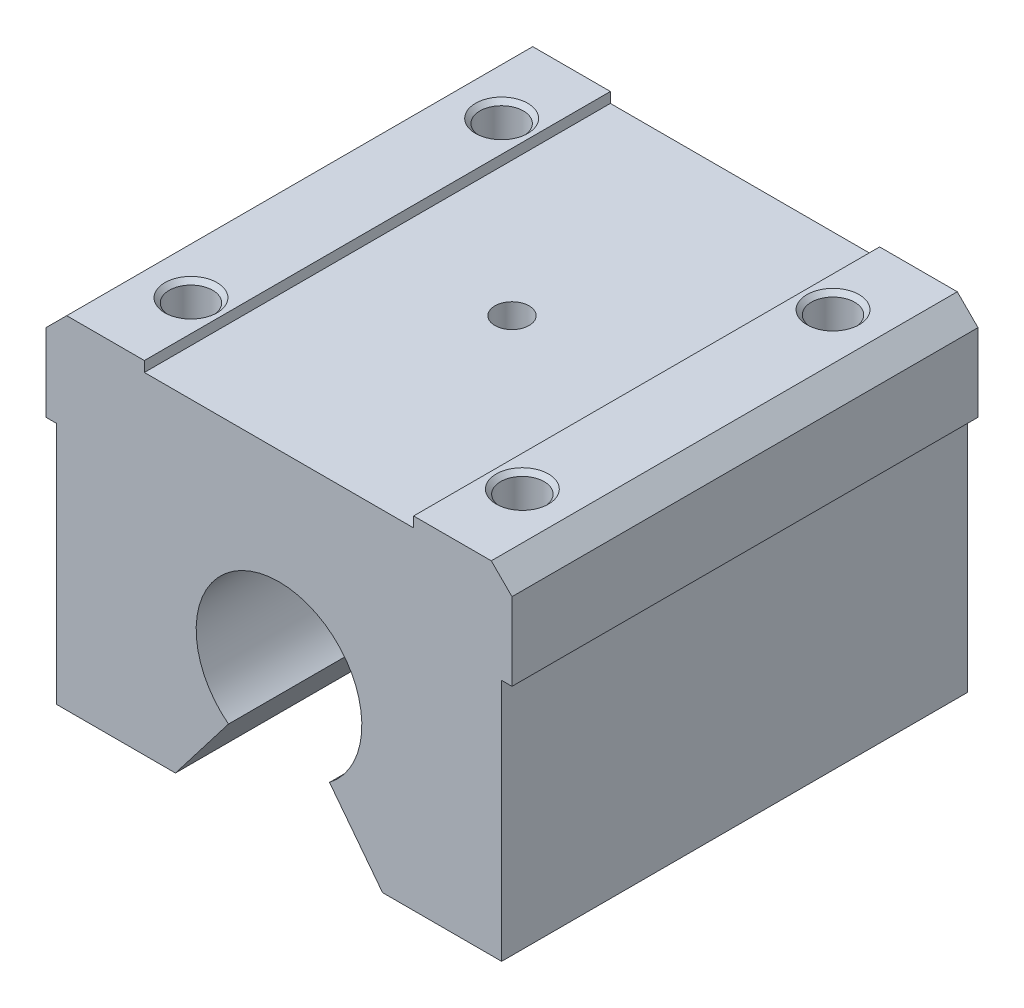
SolidWorks part; units mm, degrees
ref_plane "Front Plane" through (0, 0, 0) normal (0, 0, 1) x (1, 0, 0)
ref_plane "Top Plane" through (0, 0, 0) normal (0, 1, 0) x (1, 0, 0)
ref_plane "Right Plane" through (0, 0, 0) normal (1, 0, 0) x (0, 0, -1)
sketch "Sketch1" plane through (0, 0, 0) normal (0, 0, 1) x (1, 0, 0)
  line L0 (0, 0) -> (0, 37.2391) construction
  line L1 (0, 0) -> (27.9005, 0) construction
  line L2 (10, -13) -> (21.5, -13)
  line L3 (21.5, -13) -> (21.5, 10.5)
  line L4 (21.5, 10.5) -> (22.5, 10.5)
  line L5 (22.5, 10.5) -> (22.5, 18)
  line L6 (22.5, 18) -> (20.5, 20)
  line L7 (20.5, 20) -> (13, 20)
  line L8 (13, 20) -> (13, 19)
  line L9 (13, 19) -> (0, 19)
  line L10 (21.5, 10.5) -> (21.5, 19) construction
  line L11 (0, 8) -> (0, 19)
  line L12 (4.8777, -6.341) -> (10, -13)
  line L13 (16, 26.894) -> (16, 15.2711) construction
  circle A0 centre (0, 0) radius 8
  dimension "D1" = 16
  dimension "D2" = 45
  dimension "D3" = 33
  dimension "D4" = 20
  dimension "D5" = 45
  dimension "D6" = 1
  dimension "D7" = 1
  dimension "D8" = 20
  dimension "D9" = 32
  dimension "D10" = 6
sketch "Sketch2" plane through (0, 0, 0) normal (0, 0, 1) x (1, 0, 0)
  line L0 (0, 8) -> (0, 19) construction
  line L1 (13, 19) -> (0, 19) construction
  line L2 (13, 20) -> (13, 19) construction
  line L3 (20.5, 20) -> (13, 20) construction
  line L4 (22.5, 18) -> (20.5, 20) construction
  line L5 (22.5, 10.5) -> (22.5, 18) construction
  line L6 (21.5, 10.5) -> (22.5, 10.5) construction
  line L7 (21.5, -13) -> (21.5, 10.5) construction
  line L8 (10, -13) -> (21.5, -13) construction
  line L9 (4.8777, -6.341) -> (10, -13) construction
  line L10 (0, 8) -> (0, 19) construction
  line L11 (13, 19) -> (-13, 19)
  line L12 (13, 20) -> (13, 19)
  line L13 (20.5, 20) -> (13, 20)
  line L14 (22.5, 18) -> (20.5, 20)
  line L15 (22.5, 10.5) -> (22.5, 18)
  line L16 (21.5, 10.5) -> (22.5, 10.5)
  line L17 (21.5, -13) -> (21.5, 10.5)
  line L18 (10, -13) -> (21.5, -13)
  line L19 (4.8777, -6.341) -> (10, -13)
  line L20 (-4.8777, -6.341) -> (-10, -13)
  line L21 (-10, -13) -> (-21.5, -13)
  line L22 (-21.5, -13) -> (-21.5, 10.5)
  line L23 (-21.5, 10.5) -> (-22.5, 10.5)
  line L24 (-22.5, 10.5) -> (-22.5, 18)
  line L25 (-22.5, 18) -> (-20.5, 20)
  line L26 (-20.5, 20) -> (-13, 20)
  line L27 (-13, 20) -> (-13, 19)
  circle A1 centre (0, 0) radius 8
  arc A2 (4.8777, -6.341) -> (-4.8777, -6.341) centre (0, 0) ccw
  dimension "D1" = 0
extrude "Boss-Extrude1" add sketch "Sketch2" along normal mid plane 45
hole_wizard "M5 Tapped Hole1" positions "Sketch3" profile "Sketch4" tap size "M5" standard "ISO"
sketch "Sketch3" plane through (0, 20, 0) normal (0, 1, 0) x (1, 0, 0)
  line L0 (0, 0) -> (0, 23.9789) construction
  line L1 (-8, 0) -> (8, 0) construction
  line L4 (0, 0) -> (-26.7272, 0) construction
  point P0 (-16, 15)
  point P14 (16, 15)
  point P16 (-16, -15)
  point P17 (16, -15)
  dimension "D1" = 32
  dimension "D2" = 30
sketch "Sketch4" plane through (-16, 20, -15) normal (1, 0, 0) x (0, 0, 1)
  line L0 (0, 0) -> (0, 13.6618)
  line L1 (0, 13.6618) -> (2.1, 12.4)
  line L2 (2.1, 12.4) -> (2.1, 0.425)
  line L3 (2.1, 0.425) -> (2.525, 0)
  line L5 (2.525, 0) -> (0, 0)
  line L6 (-2.1, 0.425) -> (-2.525, 0) construction
  line L10 (0, 13.6618) -> (-2.1, 12.4) construction
  line L11 (0, -6.35) -> (0, 107.95) construction
  dimension "Tap Drill Dia." = 4.2
  dimension "Tap Drill Depth" = 12.4
  dimension "Near C'Sink Dia." = 5.05
  dimension "Near C'Sink Angle" = 90
  dimension "Drill Angle" = 118
cosmetic thread "Hole Thread1" parameters "D1"=10, "D2"=5
cosmetic thread "Hole Thread2" parameters "D1"=10, "D2"=5
cosmetic thread "Hole Thread3" parameters "D1"=10, "D2"=5
cosmetic thread "Hole Thread4" parameters "D1"=10, "D2"=5
sketch "Sketch5" [suppressed] plane through (0, 0, 0) normal (0, 0, 1) x (1, 0, 0)
  circle A0 centre (0, 0) radius 8 construction
  circle A1 centre (0, 0) radius 8
extrude "Boss-Extrude2" [suppressed] add sketch "Sketch5" along normal mid plane 600
ref_plane "Plane1" [suppressed] through (0, -8, 0) normal (0, -1, 0) x (-1, 0, 0)
hole_wizard "M5 Tapped Hole2" [suppressed] positions "Sketch6" profile "Sketch7" tap size "M5" standard "ISO"
sketch "Sketch6" plane through (0, -8, 0) normal (0, -1, 0) x (-1, 0, 0)
  line L0 (0, 0) -> (57.0659, 0) construction
  point P0 (0, 75)
  point P10 (0, 225)
  point P16 (0, -75)
  point P17 (0, -225)
  dimension "D1" = 150
  dimension "D2" = 150
sketch "Sketch7" plane through (0, -8, -75) normal (1, 0, 0) x (0, 0, -1)
  line L0 (0, 0) -> (0, 13.6618)
  line L1 (0, 13.6618) -> (2.1, 12.4)
  line L2 (2.1, 12.4) -> (2.1, 0.425)
  line L3 (2.1, 0.425) -> (2.525, 0)
  line L5 (2.525, 0) -> (0, 0)
  line L6 (-2.1, 0.425) -> (-2.525, 0) construction
  line L10 (0, 13.6618) -> (-2.1, 12.4) construction
  line L11 (0, -6.35) -> (0, 107.95) construction
  dimension "Tap Drill Dia." = 4.2
  dimension "Tap Drill Depth" = 12.4
  dimension "Near C'Sink Dia." = 5.05
  dimension "Near C'Sink Angle" = 90
  dimension "Drill Angle" = 118
cosmetic thread "Hole Thread5" [suppressed] parameters "D1"=10, "D2"=5
cosmetic thread "Hole Thread6" [suppressed] parameters "D1"=10, "D2"=5
cosmetic thread "Hole Thread7" [suppressed] parameters "D1"=10, "D2"=5
cosmetic thread "Hole Thread8" [suppressed] parameters "D1"=10, "D2"=5
sketch "Sketch8" [suppressed] plane through (0, 0, 0) normal (0, 0, 1) x (1, 0, 0)
  line L0 (4.5, -6.6144) -> (7.5, -11.8105)
  line L1 (7.5, -11.8105) -> (7.5, -15)
  line L2 (7.5, -15) -> (-7.5, -15)
  line L3 (0, -15) -> (0, -8) construction
  line L4 (-7.5, -11.8105) -> (-7.5, -15)
  line L5 (-4.5, -6.6144) -> (-7.5, -11.8105)
  line L6 (1.5, -9) -> (-1.5, -9)
  line L7 (-1.5, -9) -> (-1.5, -7.8581)
  line L8 (1.5, -9) -> (1.5, -7.8581)
  circle A0 centre (0, 0) radius 8 construction
  arc A1 (-4.5, -6.6144) -> (-1.5, -7.8581) centre (0, 0) ccw
  arc A2 (1.5, -7.8581) -> (4.5, -6.6144) centre (0, 0) ccw
  point P14 (0, -9)
  dimension "D1" = 15
  dimension "D2" = 30
  dimension "D3" = 15
  dimension "D4" = 9
  dimension "D5" = 1
  dimension "D6" = 3
extrude "Boss-Extrude3" [suppressed] add sketch "Sketch8" along normal mid plane 540 separate body
sketch "Sketch9" [suppressed] plane through (0, 0, 0) normal (0, 0, 1) x (1, 0, 0)
  line L0 (-7.5, -15) -> (7.5, -15) construction
  line L1 (-10, -15) -> (10, -15)
  line L2 (-10, -15) -> (-10, -72)
  line L3 (-10, -72) -> (10, -72)
  line L4 (10, -15) -> (10, -72)
  line L5 (0, 0) -> (0, -52.7462) construction
  dimension "D1" = 20
  dimension "D2" = 72
extrude "Boss-Extrude4" [suppressed] add sketch "Sketch9" along normal mid plane 592
hole_wizard "M5 Clearance Hole1" [suppressed] positions "Sketch10" profile "Sketch11" hole size "M5" standard "ISO"
sketch "Sketch10" plane through (0, -15, 0) normal (0, -1, 0) x (-1, 0, 0)
  point P0 (0, 225)
  point P3 (0, 75)
  point P6 (0, -75)
  point P9 (0, -225)
sketch "Sketch11" plane through (0, -15, -225) normal (1, 0, 0) x (0, 0, -1)
  line L0 (0, 0) -> (0, 23)
  line L1 (0, 23) -> (2.75, 23)
  line L2 (2.75, 23) -> (2.75, 0)
  line L5 (2.75, 0) -> (0, 0)
  line L11 (0, -6.35) -> (0, 107.95) construction
  dimension "Thru Hole Dia." = 5.5
  dimension "Thru Hole Depth" = 23
hole_wizard "CBORE for M5 Hex Socket Head Cap Screw1" [suppressed] positions "Sketch12" profile "Sketch13" counterbore size "M5" standard "ISO"
sketch "Sketch12" plane through (0, -72, 0) normal (0, -1, 0) x (-1, 0, 0)
  point P0 (0, 225)
  point P5 (0, 75)
  point P8 (0, -75)
  point P11 (0, -225)
sketch "Sketch13" plane through (0, -72, -225) normal (1, 0, 0) x (0, 0, -1)
  line L0 (0, 0) -> (0, 80)
  line L1 (0, 80) -> (2.75, 80)
  line L3 (2.75, 80) -> (2.75, 22)
  line L4 (2.75, 22) -> (5, 22)
  line L5 (5, 22) -> (5, 0)
  line L7 (5, 0) -> (0, 0)
  line L11 (0, -6.35) -> (0, 107.95) construction
  dimension "Thru Hole Dia." = 5.5
  dimension "Thru Hole Depth" = 80
  dimension "C'Bore Dia." = 10
  dimension "C'Bore Depth" = 22
hole_wizard "CBORE for M5 Hex Socket Head Cap Screw2" [suppressed] positions "Sketch14" profile "Sketch15" counterbore size "M5" standard "ISO"
sketch "Sketch14" plane through (-10, 0, 0) normal (-1, 0, 0) x (0, 0, 1)
  line L0 (0, 0) -> (0, 78.9469) construction
  point P0 (283, -27)
  point P2 (257, -27)
  point P4 (257, -63)
  point P6 (283, -63)
  point P18 (-283, -63)
  point P19 (-257, -63)
  point P20 (-257, -27)
  point P21 (-283, -27)
  dimension "D1" = 36
  dimension "D2" = 27
  dimension "D3" = 26
  dimension "D4" = 566
sketch "Sketch15" plane through (-10, -27, 283) normal (0, 1, 0) x (0, 0, 1)
  line L0 (0, 0) -> (0, 20)
  line L1 (0, 20) -> (2.9, 20)
  line L3 (2.9, 20) -> (2.9, 5.4)
  line L4 (2.9, 5.4) -> (5, 5.4)
  line L5 (5, 5.4) -> (5, 0)
  line L7 (5, 0) -> (0, 0)
  line L11 (0, -6.35) -> (0, 107.95) construction
  dimension "Thru Hole Dia." = 5.8
  dimension "Thru Hole Depth" = 20
  dimension "C'Bore Dia." = 10
  dimension "C'Bore Depth" = 5.4
sketch "Sketch16" [suppressed] plane through (0, 0, 0) normal (0, 1, 0) x (1, 0, 0)
  line L0 (0, 75) -> (-41.5156, 75) construction
  line L2 (45.7461, 262) -> (-41.5156, 262)
  line L3 (45.7461, 262) -> (45.7461, -112)
  line L4 (45.7461, -112) -> (-41.5156, -112)
  line L5 (-41.5156, 262) -> (-41.5156, -112)
  dimension "D1" = 374
extrude "Cut-Extrude1" [suppressed] cut sketch "Sketch16" against normal through all both and the other way through all flip side to cut
delete or keep bodies "Body-Delete/Keep 1" [suppressed] type keep bodies bodies 107
delete or keep bodies "Body-Delete/Keep 2" [suppressed] type keep bodies bodies 110
pattern_linear "LPattern1" [suppressed] count 2 spacing 100
sketch "Sketch17" [suppressed] plane through (0, 0, 22.5) normal (0, 0, 1) x (1, 0, 0)
  line L0 (0, 0) -> (0, -15.7889) construction
  line L17 (4.8777, -6.341) -> (10, -13)
  line L18 (10, -13) -> (21.5, -13)
  line L19 (21.5, -13) -> (21.5, 10.5)
  line L20 (21.5, 10.5) -> (22.5, 10.5)
  line L21 (22.5, 10.5) -> (22.5, 18)
  line L22 (22.5, 18) -> (20.5, 20)
  line L23 (20.5, 20) -> (13, 20)
  line L24 (13, 20) -> (13, 19)
  line L25 (13, 19) -> (-13, 19)
  line L26 (-13, 19) -> (-13, 20)
  line L27 (-13, 20) -> (-20.5, 20)
  line L28 (-20.5, 20) -> (-22.5, 18)
  line L29 (-22.5, 18) -> (-22.5, 10.5)
  line L30 (-22.5, 10.5) -> (-21.5, 10.5)
  line L31 (-21.5, 10.5) -> (-21.5, -13)
  line L32 (-21.5, -13) -> (-10, -13)
  line L33 (-10, -13) -> (-4.8777, -6.341)
  line L34 (4.8777, -6.341) -> (10, -13)
  line L35 (10, -13) -> (21.5, -13)
  line L36 (21.5, -13) -> (21.5, 10.5)
  line L37 (21.5, 10.5) -> (22.5, 10.5)
  line L38 (22.5, 10.5) -> (22.5, 18)
  line L39 (22.5, 18) -> (20.5, 20)
  line L40 (20.5, 20) -> (13, 20)
  line L41 (13, 20) -> (13, 19)
  line L42 (13, 19) -> (-13, 19)
  line L43 (-13, 19) -> (-13, 20)
  line L44 (-13, 20) -> (-20.5, 20)
  line L45 (-20.5, 20) -> (-22.5, 18)
  line L46 (-22.5, 18) -> (-22.5, 10.5)
  line L47 (-22.5, 10.5) -> (-21.5, 10.5)
  line L48 (-21.5, 10.5) -> (-21.5, -13)
  line L49 (-21.5, -13) -> (-10, -13)
  line L50 (-10, -13) -> (-4.8777, -6.341)
  arc A1 (4.8777, -6.341) -> (-4.8777, -6.341) centre (0, 0) ccw
  arc A2 (4.8777, -6.341) -> (-4.8777, -6.341) centre (0, 0) ccw
  dimension "D2" = 9.7554
  dimension "D3" = 37.569
  dimension "D1" = 0
sketch "Sketch18" [suppressed] plane through (-10, 0, 0) normal (-1, 0, 0) x (0, 0, 1)
  line L0 (-283, -27) -> (-257, -27) construction
  line L1 (-283, -63) -> (-257, -63) construction
  line L2 (0, 0) -> (0, -129.1435) construction
  line L3 (-270, -63) -> (-270, -27) construction
sketch "Sketch19" [suppressed] plane through (-10, 0, 0) normal (-1, 0, 0) x (0, 0, 1)
  line L0 (-296, -15) -> (-296, -72) construction
  line L1 (296, -72) -> (-296, -72) construction
  line L2 (-296, -15) -> (-296, -72)
  line L3 (296, -15) -> (-296, -15) construction
  point P0 (-283, -63)
  point P1 (-257, -63)
  point P3 (-257, -27)
  point P5 (-283, -27)
  dimension "D1" = 13
  dimension "D2" = 39
  dimension "D3" = 45
  dimension "D4" = 9
  dimension "D5" = 57
  dimension "D6" = 12
sketch "Sketch20" [suppressed] plane through (-4.6, 0, 0) normal (-1, 0, 0) x (0, 0, 1)
  line L0 (-283, -28.5) -> (-283, -25.5) construction
  line L1 (-288, -28.5) -> (-288, -25.5)
  line L2 (-278, -28.5) -> (-278, -25.5)
  line L3 (-283, -27) -> (-257, -27) construction
  line L4 (-257, -27) -> (-257, -63) construction
  line L5 (-257, -45) -> (-270, -45) construction
  line L6 (-270, -45) -> (-270, -27) construction
  line L7 (-257, -28.5) -> (-257, -25.5) construction
  line L8 (-252, -28.5) -> (-252, -25.5)
  line L9 (-262, -28.5) -> (-262, -25.5)
  line L10 (-283, -61.5) -> (-283, -64.5) construction
  line L11 (-288, -61.5) -> (-288, -64.5)
  line L12 (-278, -61.5) -> (-278, -64.5)
  line L13 (-257, -61.5) -> (-257, -64.5) construction
  line L14 (-252, -61.5) -> (-252, -64.5)
  line L15 (-262, -61.5) -> (-262, -64.5)
  line L16 (0, 0) -> (0, -138.9262) construction
  line L17 (283, -28.5) -> (283, -25.5) construction
  line L18 (288, -28.5) -> (288, -25.5)
  line L19 (278, -28.5) -> (278, -25.5)
  line L20 (257, -28.5) -> (257, -25.5) construction
  line L21 (252, -28.5) -> (252, -25.5)
  line L22 (262, -28.5) -> (262, -25.5)
  line L23 (283, -61.5) -> (283, -64.5) construction
  line L24 (288, -61.5) -> (288, -64.5)
  line L25 (278, -61.5) -> (278, -64.5)
  line L26 (257, -61.5) -> (257, -64.5) construction
  line L27 (252, -61.5) -> (252, -64.5)
  line L28 (262, -61.5) -> (262, -64.5)
  arc A0 (-288, -28.5) -> (-278, -28.5) centre (-283, -28.5) ccw
  circle A1 centre (-283, -27) radius 5
  circle A2 centre (-283, -27) radius 5 construction
  arc A3 (-278, -25.5) -> (-288, -25.5) centre (-283, -25.5) ccw
  arc A4 (-252, -28.5) -> (-262, -28.5) centre (-257, -28.5) cw
  arc A5 (-262, -25.5) -> (-252, -25.5) centre (-257, -25.5) cw
  arc A6 (-288, -61.5) -> (-278, -61.5) centre (-283, -61.5) cw
  arc A7 (-278, -64.5) -> (-288, -64.5) centre (-283, -64.5) cw
  arc A8 (-252, -61.5) -> (-262, -61.5) centre (-257, -61.5) ccw
  arc A9 (-262, -64.5) -> (-252, -64.5) centre (-257, -64.5) ccw
  arc A10 (288, -28.5) -> (278, -28.5) centre (283, -28.5) cw
  arc A11 (278, -25.5) -> (288, -25.5) centre (283, -25.5) cw
  arc A12 (252, -28.5) -> (262, -28.5) centre (257, -28.5) ccw
  arc A13 (262, -25.5) -> (252, -25.5) centre (257, -25.5) ccw
  arc A14 (288, -61.5) -> (278, -61.5) centre (283, -61.5) ccw
  arc A15 (278, -64.5) -> (288, -64.5) centre (283, -64.5) ccw
  arc A16 (252, -61.5) -> (262, -61.5) centre (257, -61.5) cw
  arc A17 (262, -64.5) -> (252, -64.5) centre (257, -64.5) cw
  point P5 (-283, -27)
  point P19 (-257, -27)
  point P26 (-283, -63)
  point P33 (-257, -63)
  point P43 (283, -27)
  point P50 (257, -27)
  point P57 (283, -63)
  point P64 (257, -63)
  dimension "D2" = 3
  dimension "D1" = 0
extrude "Cut-Extrude2" [suppressed] cut sketch "Sketch20" along normal through all
sketch "Sketch21" [suppressed] plane through (-4.6, 0, 0) normal (-1, 0, 0) x (0, 0, 1)
  line L0 (-283, -25.5) -> (-283, -28.5) construction
  line L1 (-280.1, -25.5) -> (-280.1, -28.5)
  line L2 (-285.9, -25.5) -> (-285.9, -28.5)
  line L3 (-257, -27) -> (-283, -27) construction
  line L4 (-270, -27) -> (-270, -45) construction
  line L5 (-257, -27) -> (-257, -63) construction
  line L6 (-270, -45) -> (-257, -45) construction
  line L7 (-257, -25.5) -> (-257, -28.5) construction
  line L8 (-259.9, -25.5) -> (-259.9, -28.5)
  line L9 (-254.1, -25.5) -> (-254.1, -28.5)
  line L10 (-283, -64.5) -> (-283, -61.5) construction
  line L11 (-280.1, -64.5) -> (-280.1, -61.5)
  line L12 (-285.9, -64.5) -> (-285.9, -61.5)
  line L13 (-257, -64.5) -> (-257, -61.5) construction
  line L14 (-259.9, -64.5) -> (-259.9, -61.5)
  line L15 (-254.1, -64.5) -> (-254.1, -61.5)
  line L16 (0, 0) -> (0, -103.0804) construction
  line L17 (283, -25.5) -> (283, -28.5) construction
  line L18 (280.1, -25.5) -> (280.1, -28.5)
  line L19 (285.9, -25.5) -> (285.9, -28.5)
  line L20 (257, -25.5) -> (257, -28.5) construction
  line L21 (259.9, -25.5) -> (259.9, -28.5)
  line L22 (254.1, -25.5) -> (254.1, -28.5)
  line L23 (283, -64.5) -> (283, -61.5) construction
  line L24 (280.1, -64.5) -> (280.1, -61.5)
  line L25 (285.9, -64.5) -> (285.9, -61.5)
  line L26 (257, -64.5) -> (257, -61.5) construction
  line L27 (259.9, -64.5) -> (259.9, -61.5)
  line L28 (254.1, -64.5) -> (254.1, -61.5)
  arc A0 (-280.1, -25.5) -> (-285.9, -25.5) centre (-283, -25.5) ccw
  arc A1 (-285.9, -28.5) -> (-280.1, -28.5) centre (-283, -28.5) ccw
  circle A2 centre (-283, -27) radius 2.9 construction
  arc A3 (-278, -25.5) -> (-288, -25.5) centre (-283, -25.5) ccw construction
  arc A4 (-259.9, -25.5) -> (-254.1, -25.5) centre (-257, -25.5) cw
  arc A5 (-254.1, -28.5) -> (-259.9, -28.5) centre (-257, -28.5) cw
  arc A6 (-280.1, -64.5) -> (-285.9, -64.5) centre (-283, -64.5) cw
  arc A7 (-285.9, -61.5) -> (-280.1, -61.5) centre (-283, -61.5) cw
  arc A8 (-259.9, -64.5) -> (-254.1, -64.5) centre (-257, -64.5) ccw
  arc A9 (-254.1, -61.5) -> (-259.9, -61.5) centre (-257, -61.5) ccw
  arc A10 (280.1, -25.5) -> (285.9, -25.5) centre (283, -25.5) cw
  arc A11 (285.9, -28.5) -> (280.1, -28.5) centre (283, -28.5) cw
  arc A12 (259.9, -25.5) -> (254.1, -25.5) centre (257, -25.5) ccw
  arc A13 (254.1, -28.5) -> (259.9, -28.5) centre (257, -28.5) ccw
  arc A14 (280.1, -64.5) -> (285.9, -64.5) centre (283, -64.5) ccw
  arc A15 (285.9, -61.5) -> (280.1, -61.5) centre (283, -61.5) ccw
  arc A16 (259.9, -64.5) -> (254.1, -64.5) centre (257, -64.5) cw
  arc A17 (254.1, -61.5) -> (259.9, -61.5) centre (257, -61.5) cw
  point P2 (-283, -27)
  point P23 (-257, -27)
  point P30 (-283, -63)
  point P37 (-257, -63)
  point P47 (283, -27)
  point P54 (257, -27)
  point P61 (283, -63)
  point P68 (257, -63)
extrude "Cut-Extrude3" [suppressed] cut sketch "Sketch21" against normal through all
sketch "Sketch22" plane through (0, 19, 0) normal (0, 1, 0) x (1, 0, 0)
  point P0 (0, 0)
hole_wizard "M4x0.7 Tapped Hole1" positions "Sketch23" profile "Sketch24" tap size "M4x0.7" standard "ANSI Metric"
sketch "Sketch23" plane through (0, 19, 0) normal (0, 1, 0) x (1, 0, 0)
  point P0 (0, 0)
sketch "Sketch24" plane through (0, 19, 0) normal (1, 0, 0) x (0, 0, 1)
  line L0 (0, 0) -> (0, 11.0914)
  line L1 (0, 11.0914) -> (1.65, 10.1)
  line L2 (1.65, 10.1) -> (1.65, 0)
  line L5 (1.65, 0) -> (0, 0)
  line L10 (0, 11.0914) -> (-1.65, 10.1) construction
  line L11 (0, -6.35) -> (0, 107.95) construction
  dimension "Tap Drill Dia." = 3.3
  dimension "Tap Drill Depth" = 10.1
  dimension "Drill Angle" = 118
cosmetic thread "Hole Thread9" parameters "D1"=8, "D2"=4
sketch "Sketch25" plane through (-21.5, 0, 0) normal (-1, 0, 0) x (0, 0, 1)
  point P0 (0, 0)
hole_wizard "M6x1.0 Tapped Hole1" positions "Sketch26" profile "Sketch27" tap size "M6x1.0" standard "ANSI Metric"
sketch "Sketch26" plane through (-21.5, 0, 0) normal (-1, 0, 0) x (0, 0, 1)
  point P0 (0, 0)
sketch "Sketch27" plane through (-21.5, 0, 0) normal (0, 1, 0) x (0, 0, 1)
  line L0 (0, 0) -> (0, 16.5022)
  line L1 (0, 16.5022) -> (2.5, 15)
  line L2 (2.5, 15) -> (2.5, 0)
  line L5 (2.5, 0) -> (0, 0)
  line L10 (0, 16.5022) -> (-2.5, 15) construction
  line L11 (0, -6.35) -> (0, 107.95) construction
  dimension "Tap Drill Dia." = 5
  dimension "Tap Drill Depth" = 15
  dimension "Drill Angle" = 118
cosmetic thread "Hole Thread10" parameters "D1"=12, "D2"=6
chamfer "Chamfer1" [suppressed] distance 0.5 angle 45
chamfer "Chamfer2" [suppressed] distance 0.5 angle 45
